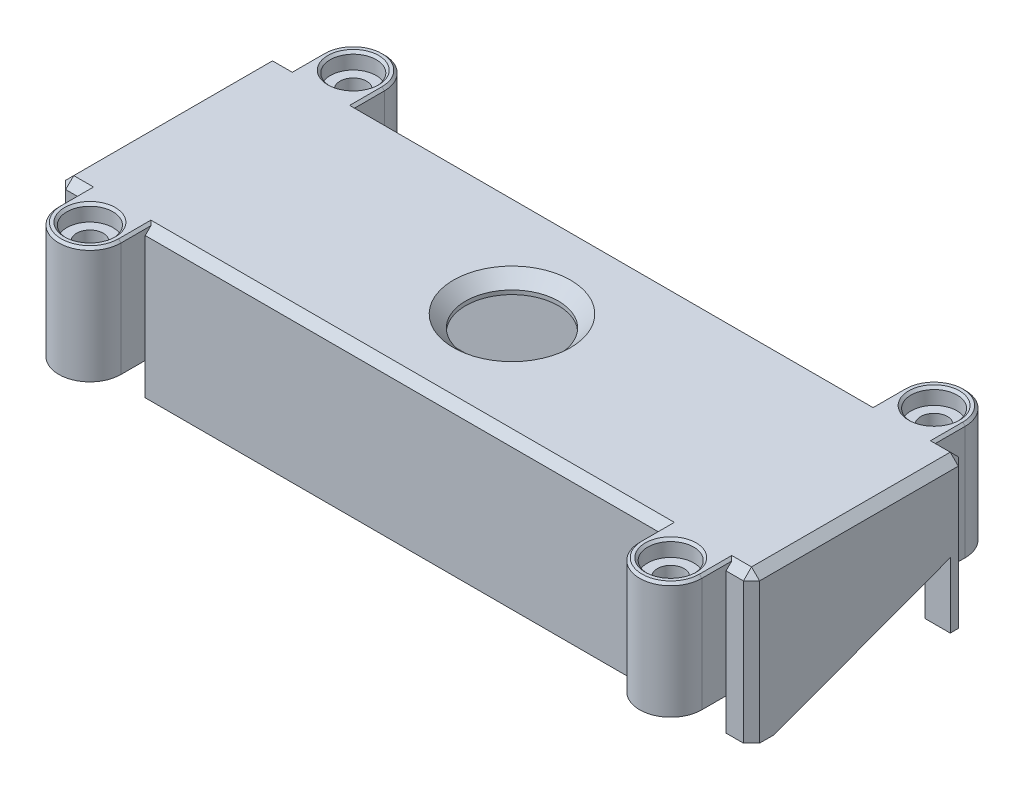
SolidWorks part; units mm, degrees
ref_plane "Front Plane" through (0, 0, 0) normal (0, 0, 1) x (1, 0, 0)
ref_plane "Top Plane" through (0, 0, 0) normal (0, 1, 0) x (1, 0, 0)
ref_plane "Right Plane" through (0, 0, 0) normal (1, 0, 0) x (0, 0, -1)
sketch "Sketch1" plane through (0, 0, 0) normal (0, 1, 0) x (1, 0, 0)
  line L1 (0, 0) -> (85.9, 0)
  line L2 (0, 0) -> (0, 26.6)
  line L3 (0, 26.6) -> (85.9, 26.6)
  line L4 (85.9, 0) -> (85.9, 26.6)
  dimension "D1" = 85.9
  dimension "D2" = 26.6
extrude "Boss-Extrude1" add sketch "Sketch1" along normal blind 18.4
shell "Shell1" thickness 2
sketch "Sketch2" plane through (0, 18.4, 0) normal (0, 1, 0) x (1, 0, 0)
  line L0 (0, 13.3) -> (85.9, 13.3) construction
  line L4 (0, 26.6) -> (0, 0) construction
  line L5 (85.9, 0) -> (85.9, 26.6) construction
  circle A0 centre (42.95, 13.3) radius 5.75
  dimension "D1" = 11.5
extrude "Cut-Extrude1" cut sketch "Sketch2" against normal through all
sketch "Sketch3" plane through (85.9, 0, 0) normal (1, 0, 0) x (0, 0, -1)
  line L0 (0, 18.4) -> (0, 0) construction
  line L1 (0, 0) -> (26.6, 0) construction
  line L2 (2.8125, 0) -> (24.6, 8.0872)
  line L4 (24.6, 8.0872) -> (24.6, 0)
  line L5 (24.6, 0) -> (2.8125, 0)
  line L6 (26.6, 18.4) -> (26.6, 0) construction
  dimension "D1" = 2.8125
  dimension "D2" = 69.636
  dimension "D3" = 2
extrude "Cut-Extrude2" cut sketch "Sketch3" against normal through all
chamfer "Chamfer1" distance 1.5 angle 45 1 edges at (42.95, 18.4, -7.55)
sketch "Sketch4" plane through (0, 18.4, 0) normal (0, 1, 0) x (1, 0, 0)
  line L0 (0, 26.6) -> (0, 0) construction
  line L1 (0, 0) -> (85.9, 0) construction
  line L2 (85.9, 26.6) -> (0, 26.6) construction
  line L3 (3.15, 29.6) -> (3.15, 26.6)
  line L4 (3.15, 26.6) -> (10.85, 26.6)
  line L5 (10.85, 26.6) -> (10.85, 29.6)
  line L6 (3.15, -3) -> (3.15, 0)
  line L7 (3.15, 0) -> (10.85, 0)
  line L8 (10.85, 0) -> (10.85, -3)
  line L9 (42.95, 26.6) -> (42.95, 0) construction
  line L10 (75.05, 0) -> (75.05, -3)
  line L11 (82.75, 0) -> (75.05, 0)
  line L12 (82.75, -3) -> (82.75, 0)
  line L13 (75.05, 26.6) -> (75.05, 29.6)
  line L14 (82.75, 26.6) -> (75.05, 26.6)
  line L15 (82.75, 29.6) -> (82.75, 26.6)
  circle A0 centre (7, 29.6) radius 2.85 construction
  circle A1 centre (7, -3) radius 2.85 construction
  circle A2 centre (7, 29.6) radius 3.85 construction
  circle A3 centre (7, -3) radius 3.85 construction
  arc A4 (3.15, 29.6) -> (10.85, 29.6) centre (7, 29.6) cw
  arc A5 (3.15, -3) -> (10.85, -3) centre (7, -3) ccw
  circle A6 centre (78.9, -3) radius 3.85 construction
  circle A7 centre (78.9, 29.6) radius 3.85 construction
  circle A8 centre (78.9, -3) radius 2.85 construction
  circle A9 centre (78.9, 29.6) radius 2.85 construction
  arc A10 (82.75, -3) -> (75.05, -3) centre (78.9, -3) cw
  arc A11 (82.75, 29.6) -> (75.05, 29.6) centre (78.9, 29.6) ccw
  dimension "D1" = 5.7
  dimension "D2" = 7
  dimension "D3" = 3
  dimension "D4" = 3
  dimension "D5" = 1
  dimension "D6" = 1
extrude "Boss-Extrude2" add sketch "Sketch4" against normal up to surface (18.4 mm away) up to face at (42.95, 0, -25.6)
sketch "Sketch5" plane through (0, 18.4, 0) normal (0, 1, 0) x (1, 0, 0)
  circle A0 centre (7, 29.6) radius 1.65
  circle A1 centre (7, -3) radius 1.65
  circle A2 centre (78.9, -3) radius 1.65
  circle A3 centre (78.9, 29.6) radius 1.65
  arc A4 (10.85, 29.6) -> (3.15, 29.6) centre (7, 29.6) ccw construction
  arc A5 (3.15, -3) -> (10.85, -3) centre (7, -3) ccw construction
  arc A6 (75.05, -3) -> (82.75, -3) centre (78.9, -3) ccw construction
  arc A7 (82.75, 29.6) -> (75.05, 29.6) centre (78.9, 29.6) ccw construction
  dimension "D1" = 3.3
extrude "Cut-Extrude3" cut sketch "Sketch5" against normal through all
sketch "Sketch6" plane through (0, 18.4, 0) normal (0, 1, 0) x (1, 0, 0)
  circle A0 centre (7, 29.6) radius 2.85
  circle A1 centre (78.9, 29.6) radius 2.85
  circle A2 centre (78.9, -3) radius 2.85
  circle A3 centre (7, -3) radius 2.85
  dimension "D1" = 5.7
extrude "Cut-Extrude4" cut sketch "Sketch6" against normal blind 2
chamfer "Chamfer2" distance 0.3 angle 45 4 edges at (78.9, 18.4, -26.75) (78.9, 18.4, 5.85) (7, 18.4, 5.85) (7, 18.4, -26.75)
chamfer "Chamfer3" distance 1 angle 45 12 edges at (85.9, 9.2, 0) (84.325, 18.4, 0) (85.9, 18.4, -13.3) (85.9, 9.2, -26.6) (84.325, 18.4, -26.6) (42.95, 18.4, -26.6) (42.95, 18.4, 0) (1.575, 18.4, 0) (0, 9.2, 0) (0, 9.2, -26.6) (1.575, 18.4, -26.6) (0, 18.4, -13.3)
sketch "Sketch7" plane through (0, 0, 0) normal (0, -1, 0) x (1, 0, 0)
  line L0 (82.75, 3) -> (82.75, 0) construction
  line L1 (3.15, 0) -> (82.75, 0)
  line L2 (3.15, 0) -> (3.15, 6.85)
  line L3 (3.15, 6.85) -> (82.75, 6.85)
  line L4 (82.75, 0) -> (82.75, 6.85)
  line L5 (82.75, -26.6) -> (82.75, -29.6) construction
  line L6 (3.15, -26.6) -> (82.75, -26.6)
  line L7 (3.15, -26.6) -> (3.15, -33.45)
  line L8 (3.15, -33.45) -> (82.75, -33.45)
  line L9 (82.75, -26.6) -> (82.75, -33.45)
  arc A0 (10.85, 3) -> (3.15, 3) centre (7, 3) ccw construction
  arc A1 (3.15, -29.6) -> (10.85, -29.6) centre (7, -29.6) ccw construction
extrude "Cut-Extrude5" cut sketch "Sketch7" against normal blind 4
chamfer "Chamfer4" distance 0.3 angle 45 12 edges at (3.15, 18.4, -27.6) (7, 18.4, -33.45) (10.85, 18.4, -27.6) (3.15, 18.4, 1) (7, 18.4, 6.85) (10.85, 18.4, 1) (75.05, 18.4, -27.6) (78.9, 18.4, -33.45) (82.75, 18.4, -27.6) (75.05, 18.4, 1) (78.9, 18.4, 6.85) (82.75, 18.4, 1)
sketch "Sketch8" plane through (0, 0, 0) normal (0, 0, 1) x (1, 0, 0)
  line L0 (1, 0) -> (84.9, 0) construction
  line L1 (3.15, 4) -> (10.85, 4)
  line L2 (3.15, 4) -> (3.15, 0)
  line L3 (3.15, 0) -> (10.85, 0)
  line L4 (10.85, 4) -> (10.85, 0)
  line L6 (75.05, 4) -> (82.75, 4)
  line L7 (75.05, 4) -> (75.05, 0)
  line L8 (75.05, 0) -> (82.75, 0)
  line L9 (82.75, 4) -> (82.75, 0)
extrude "Cut-Extrude6" cut sketch "Sketch8" against normal through all
